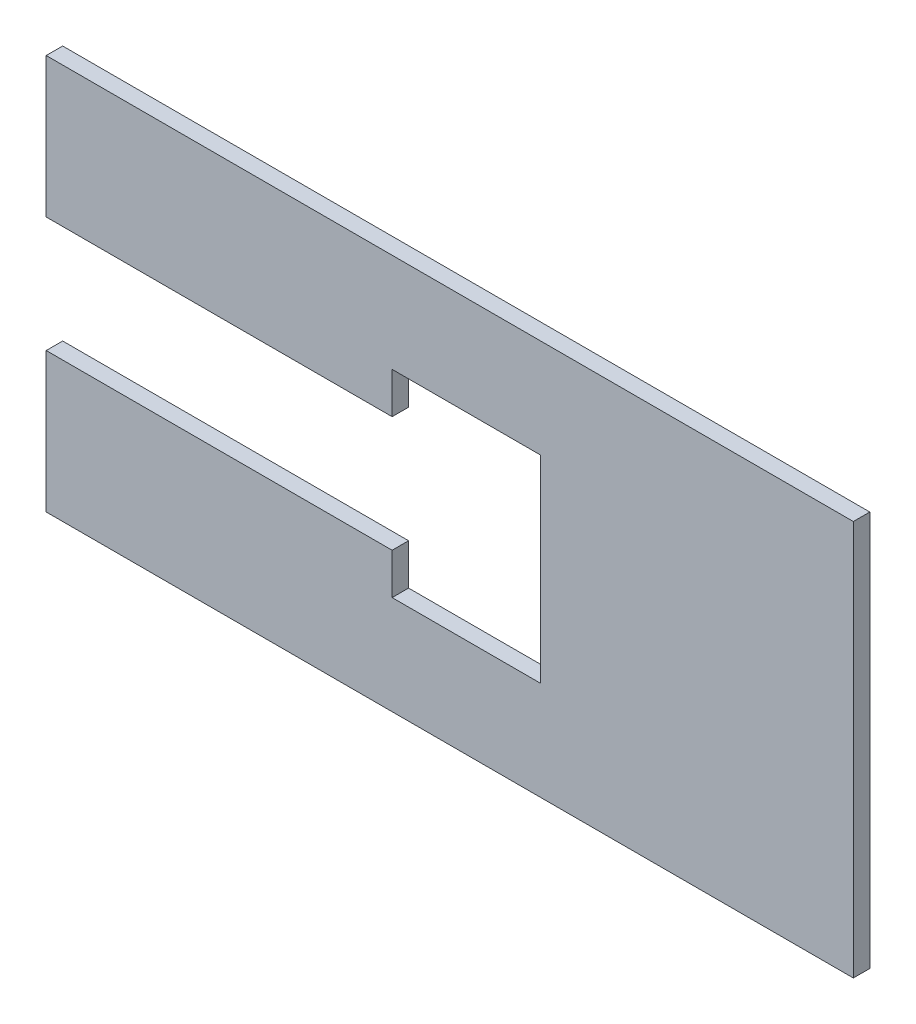
SolidWorks part; units mm, degrees
ref_plane "Plan de face" through (0, 0, 0) normal (0, 0, 1) x (1, 0, 0)
ref_plane "Plan de dessus" through (0, 0, 0) normal (0, 1, 0) x (1, 0, 0)
ref_plane "Plan de droite" through (0, 0, 0) normal (1, 0, 0) x (0, 0, -1)
sketch "Esquisse1" plane through (0, 0, 0) normal (0, 0, 1) x (1, 0, 0)
  line L1 (122.5, -60) -> (-122.5, -60)
  line L2 (122.5, -60) -> (122.5, 60)
  line L3 (122.5, 60) -> (-122.5, 60)
  line L4 (-122.5, -60) -> (-122.5, 60)
  line L5 (122.5, -60) -> (-122.5, 60) construction
  line L6 (122.5, 60) -> (-122.5, -60) construction
  point P0 (0, 0)
  dimension "D1" = 245
  dimension "D2" = 120
extrude "Boss.-Extru.1" add sketch "Esquisse1" along normal blind 5
sketch "Esquisse2" plane through (0, 0, 5) normal (0, 0, 1) x (1, 0, 0)
  line L0 (-122.5, 60) -> (-122.5, -60) construction
  line L1 (-122.5, 17.55) -> (-17.5, 17.55)
  line L2 (-122.5, 17.55) -> (-122.5, -17.55)
  line L3 (-122.5, -17.55) -> (-17.5, -17.55)
  line L5 (-17.5, 17.55) -> (-17.5, 30)
  line L6 (27.5, -30) -> (-17.5, -30)
  line L7 (27.5, -30) -> (27.5, 30)
  line L8 (27.5, 30) -> (-17.5, 30)
  line L9 (-17.5, -30) -> (-17.5, -17.55)
  line L10 (27.5, -30) -> (-17.5, 30) construction
  line L11 (27.5, 30) -> (-17.5, -30) construction
  point P6 (-122.5, 0)
  point P8 (5, 0)
  dimension "D1" = 35.1
  dimension "D2" = 105
  dimension "D3" = 45
  dimension "D4" = 60
extrude "Enlèv. mat.-Extru.1" cut sketch "Esquisse2" against normal through all
